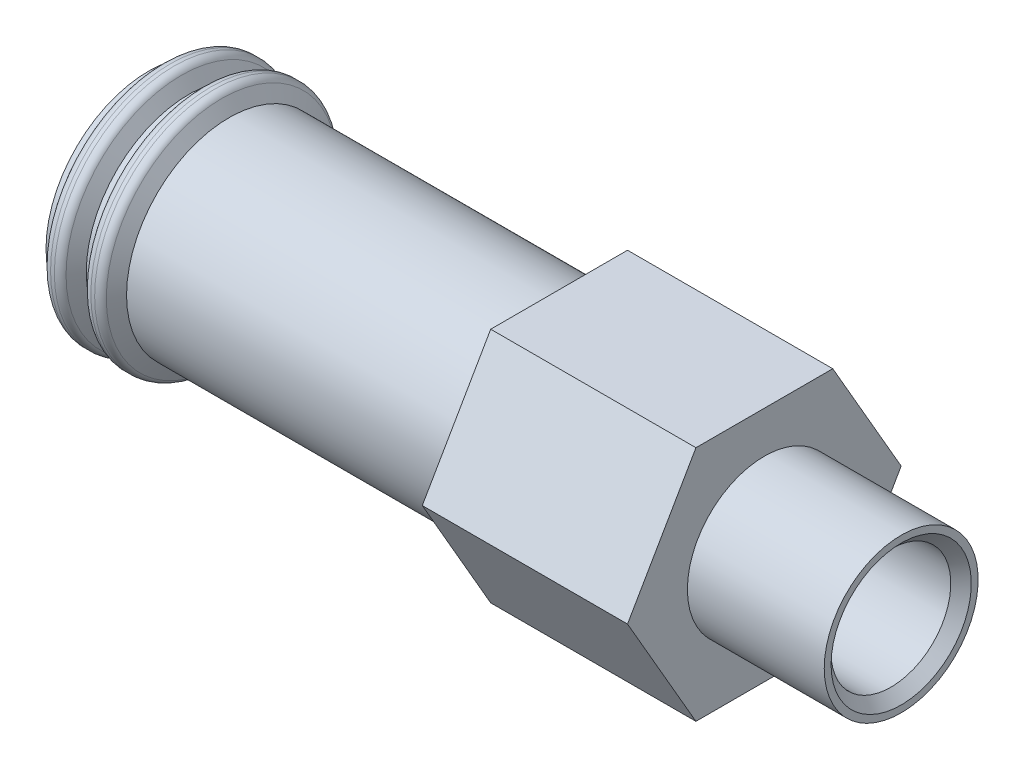
SolidWorks part; units mm, degrees
ref_plane "Plano frontal" through (0, 0, 0) normal (0, 0, 1) x (1, 0, 0)
ref_plane "Plano superior" through (0, 0, 0) normal (0, 1, 0) x (1, 0, 0)
ref_plane "Plano direito" through (0, 0, 0) normal (1, 0, 0) x (0, 0, -1)
sketch "Esboço1" plane through (0, 0, 0) normal (0, 0, 1) x (1, 0, 0)
  line L0 (-29.7219, 0) -> (34.3685, 0) construction
  line L1 (-13.3226, 3) -> (-13.1226, 3)
  line L2 (-2.5, 3) -> (-2.5, 4)
  line L3 (-2.5, 4) -> (3.5, 4)
  line L4 (3.5, 4) -> (3.5, 2.25)
  line L5 (3.5, 2.25) -> (7.5, 2.25)
  line L6 (7.5, 2.25) -> (7.5, 1.75)
  line L7 (-14.0113, 3.5) -> (-14.3, 3)
  line L8 (-14.5, 2.5) -> (-14.5, 3)
  line L9 (-10.5, 2.5) -> (-14.5, 2.5)
  line L10 (-9.201, 1.75) -> (7.5, 1.75)
  line L11 (-14.5, 2.5) -> (8.7174, 2.5) construction
  line L12 (0, 4) -> (0, 1.75) construction
  line L13 (0, 0) -> (0, 4.9732) construction
  line L14 (-10.5, 2.5) -> (-9.201, 1.75)
  line L15 (-14.0113, 3.5) -> (-13.6113, 3.5)
  line L16 (-13.6113, 3.5) -> (-13.3226, 3)
  line L17 (-13.1226, 3) -> (-12.834, 3.5)
  line L18 (-12.834, 3.5) -> (-12.434, 3.5)
  line L19 (-12.434, 3.5) -> (-12.1453, 3)
  line L20 (-12.1453, 3) -> (-2.5, 3)
  line L21 (-14.5, 3) -> (-14.3, 3)
  dimension "D12" = 60
  dimension "D1" = 5
  dimension "D2" = 4.5
  dimension "D3" = 0.5
  dimension "D4" = 22
  dimension "D5" = 8
  dimension "D6" = 12
  dimension "D7" = 6
  dimension "D8" = 4
  dimension "D9" = 6
  dimension "D10" = 7.5
  dimension "D11" = 150
  dimension "D13" = 60
  dimension "D14" = 0.5
  dimension "D15" = 0.5
  dimension "D16" = 0.4
  dimension "D17" = 0.2
  dimension "D18" = 60
  dimension "D19" = 60
  dimension "D20" = 0.5
  dimension "D21" = 0.4
  dimension "D22" = 0.2
revolve "Revolução1" add sketch "Esboço1" angle 360 about L0
sketch "Esboço2" plane through (3.5, 0, 0) normal (1, 0, 0) x (0, 0, -1)
  line L1 (4, 0) -> (2, 3.4641)
  line L2 (2, 3.4641) -> (-2, 3.4641)
  line L3 (-2, 3.4641) -> (-4, 0)
  line L4 (-4, 0) -> (-2, -3.4641)
  line L5 (-2, -3.4641) -> (2, -3.4641)
  line L6 (2, -3.4641) -> (4, 0)
  circle A0 centre (0, 0) radius 3.4641 construction
  circle A1 centre (0, 0) radius 4
  circle M2 centre (0, 0) radius 4
  dimension "D1" = 4
extrude "Corte-extrusão1" cut sketch "Esboço2" against normal up to next contours L2 M2 | L3 M2 | L4 M2 | L5 M2 | L6 M2 | L1 M2
fillet "Filete1" radius 0.25 2 edges at (-13.6113, 0, 3.5) (-14.0113, 0, 3.5)
fillet "Filete2" radius 0.25 2 edges at (-12.834, 0, 3.5) (-12.434, 0, 3.5)
chamfer "Chanfro1" distance 0.3 angle 45 1 edges at (7.5, 0, 1.75)
